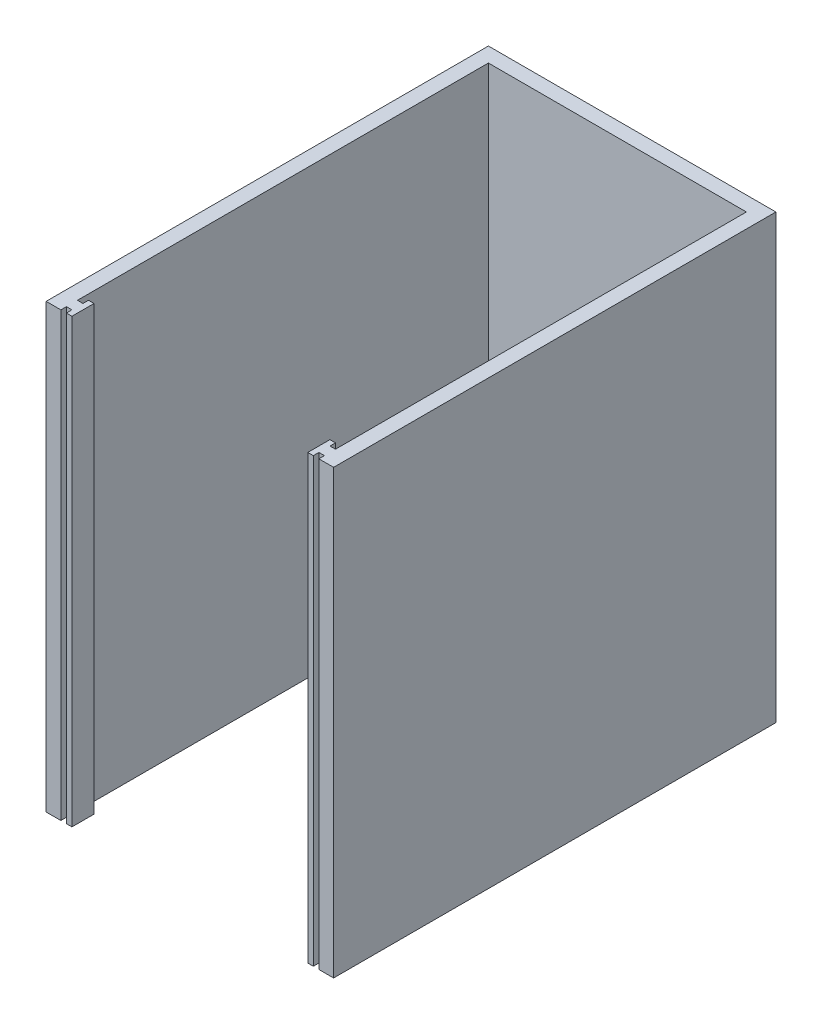
SolidWorks part; units mm, degrees
ref_plane "Plan de face" through (0, 0, 0) normal (0, 0, 1) x (1, 0, 0)
ref_plane "Plan de dessus" through (0, 0, 0) normal (0, 1, 0) x (1, 0, 0)
ref_plane "Plan de droite" through (0, 0, 0) normal (1, 0, 0) x (0, 0, -1)
sketch "Esquisse1" plane through (0, 0, 0) normal (0, 1, 0) x (1, 0, 0)
  line L0 (152.6773, 0) -> (0, 0) construction
  line L1 (0, 0) -> (0, 96.7963) construction
  line L2 (74, -120) -> (78, -120)
  line L3 (0, 0) -> (78, 0)
  line L4 (0, 0) -> (0, -120)
  line L5 (0, -120) -> (4, -120)
  line L6 (78, 0) -> (78, -120)
  line L9 (4, -4) -> (74, -4)
  line L10 (74, -120) -> (74, -118.5)
  line L11 (39, 0) -> (39, -168.7894) construction
  line L12 (5.5, -120) -> (7, -120)
  line L14 (5.5, -114) -> (7, -114)
  line L15 (7, -120) -> (7, -114)
  line L16 (5.5, -120) -> (5.5, -118.5)
  line L17 (5.5, -118.5) -> (4, -118.5)
  line L18 (5.5, -114) -> (5.5, -115.5)
  line L19 (5.5, -115.5) -> (4, -115.5)
  line L21 (72.5, -115.5) -> (74, -115.5)
  line L22 (72.5, -114) -> (72.5, -115.5)
  line L23 (72.5, -118.5) -> (74, -118.5)
  line L24 (72.5, -120) -> (72.5, -118.5)
  line L25 (71, -120) -> (71, -114)
  line L26 (72.5, -114) -> (71, -114)
  line L27 (72.5, -120) -> (71, -120)
  line L28 (74, -115.5) -> (74, -4)
  line L29 (4, -120) -> (4, -118.5)
  line L30 (4, -115.5) -> (4, -4)
  point P17 (5.5, -114.75)
  point P24 (0, 0)
  point P33 (-27.082, -87.2798)
  dimension "D1" = 120
  dimension "D2" = 78
  dimension "D3" = 70
  dimension "D4" = 1.5
  dimension "D5" = 4
  dimension "D6" = 3
  dimension "D8" = 1.5
  dimension "D9" = 1.5
  dimension "D10" = 3
extrude "Boss.-Extru.2" add sketch "Esquisse1" along normal blind 120
